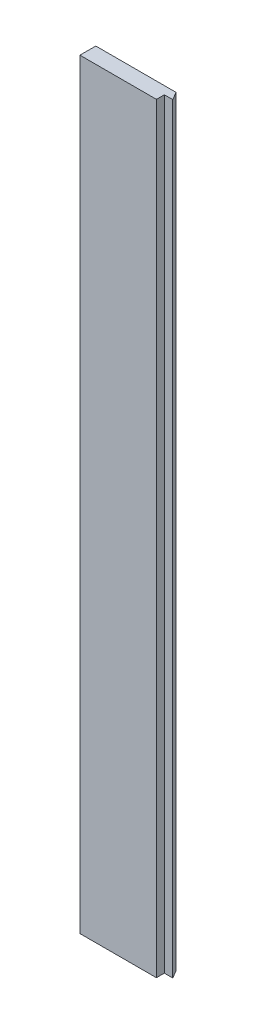
SolidWorks part; units mm, degrees
ref_plane "Front Plane" through (0, 0, 0) normal (0, 0, 1) x (1, 0, 0)
ref_plane "Top Plane" through (0, 0, 0) normal (0, 1, 0) x (1, 0, 0)
ref_plane "Right Plane" through (0, 0, 0) normal (1, 0, 0) x (0, 0, -1)
sketch "Sketch1" plane through (0, 0, 0) normal (0, 1, 0) x (1, 0, 0)
  line L0 (-60, 0) -> (-41.5, 0)
  line L1 (-60, 9) -> (60, 9)
  line L2 (-60, 9) -> (-60, -9)
  line L3 (-60, -9) -> (60, -9)
  line L4 (60, 9) -> (60, -9)
  line L5 (-60, 9) -> (60, -9) construction
  line L6 (-60, -9) -> (60, 9) construction
  line L7 (-41.5, 0) -> (-36.3038, 9)
  line L8 (-41.5, 0) -> (-41.5, 9) construction
  line L9 (60, 0) -> (54.8038, 9)
  line L10 (60, 0) -> (50.5, 0)
  line L11 (50.5, 0) -> (50.5, -9)
  line L13 (0, 9) -> (0, -9) construction
  point P0 (0, 0)
  dimension "D1" = 120
  dimension "D2" = 18
  dimension "D3" = 18.5
  dimension "D4" = 30
  dimension "D5" = 9.5
  dimension "D6" = 30
extrude "Shape" add sketch "Sketch1" along normal blind 1000
ref_plane "Plane1" [suppressed] through (-60, 790, 9) normal (0.5851, -0.811, 0) x (-0.811, -0.5851, 0)
sketch "Sketch3" [suppressed] plane through (0, 0, 9) normal (0, 0, 1) x (1, 0, 0)
  line L1 (-60, 790) -> (445, 90) construction
  line L3 (-60, 790) -> (445, 90)
  line L6 (50.5, 0) -> (60, 0)
  line L7 (60, 0) -> (60, 800)
  line L8 (60, 800) -> (50.5, 800)
  line L9 (50.5, 800) -> (50.5, 0)
  line L10 (50.5, 0) -> (60, 0)
  line L11 (60, 0) -> (60, 800)
  line L12 (60, 800) -> (50.5, 800)
  line L13 (50.5, 800) -> (50.5, 0)
  dimension "D1" = 0
extrude "Cut-Extrude1" [suppressed] cut sketch "Sketch3" against normal up to next
sketch "Sketch4" [suppressed] plane through (0, 0, 9) normal (0, 0, 1) x (1, 0, 0)
  line L0 (-170.5, 790) -> (334.5, 90) construction
  line L1 (-170.5, 790) -> (334.5, 90)
  line L6 (50.5, 0) -> (60, 0)
  line L7 (60, 0) -> (60, 800)
  line L8 (60, 800) -> (50.5, 800)
  line L9 (50.5, 800) -> (50.5, 0)
  line L10 (50.5, 0) -> (60, 0)
  line L11 (60, 0) -> (60, 800)
  line L12 (60, 800) -> (50.5, 800)
  line L13 (50.5, 800) -> (50.5, 0)
  dimension "D1" = 0
extrude "Cut-Extrude2" [suppressed] cut sketch "Sketch4" against normal through all and the other way through all
sketch "Sketch5" [suppressed] plane through (0, 0, 9) normal (0, 0, 1) x (1, 0, 0)
  line L0 (-281, 790) -> (224, 90) construction
  line L1 (-281, 790) -> (224, 90)
  line L4 (50.5, 0) -> (60, 0)
  line L5 (60, 0) -> (60, 800)
  line L6 (60, 800) -> (50.5, 800)
  line L7 (50.5, 800) -> (50.5, 0)
  line L8 (50.5, 0) -> (60, 0)
  line L9 (60, 0) -> (60, 800)
  line L10 (60, 800) -> (50.5, 800)
  line L11 (50.5, 800) -> (50.5, 0)
  dimension "D1" = 0
extrude "Cut-Extrude3" [suppressed] cut sketch "Sketch5" against normal up to next
sketch "Sketch6" [suppressed] plane through (0, 0, 9) normal (0, 0, 1) x (1, 0, 0)
  line L0 (-391.5, 790) -> (113.5, 90) construction
  line L1 (-391.5, 790) -> (113.5, 90)
  line L6 (50.5, 0) -> (60, 0)
  line L7 (60, 0) -> (60, 800)
  line L8 (60, 800) -> (50.5, 800)
  line L9 (50.5, 800) -> (50.5, 0)
  line L10 (50.5, 0) -> (60, 0)
  line L11 (60, 0) -> (60, 800)
  line L12 (60, 800) -> (50.5, 800)
  line L13 (50.5, 800) -> (50.5, 0)
  dimension "D1" = 0
extrude "Cut-Extrude4" [suppressed] cut sketch "Sketch6" against normal up to next
sketch "Sketch7" [suppressed] plane through (0, 0, 9) normal (0, 0, 1) x (1, 0, 0)
  line L0 (-502, 790) -> (3, 90) construction
  line L1 (-502, 790) -> (3, 90)
  line L2 (3, 90) -> (3, 0)
  line L3 (-60, 0) -> (50.5, 0) construction
  line L8 (50.5, 0) -> (60, 0)
  line L9 (60, 0) -> (60, 800)
  line L10 (60, 800) -> (50.5, 800)
  line L11 (50.5, 800) -> (50.5, 0)
  line L12 (50.5, 0) -> (60, 0)
  line L13 (60, 0) -> (60, 800)
  line L14 (60, 800) -> (50.5, 800)
  line L15 (50.5, 800) -> (50.5, 0)
  line M5 (-60, 0) -> (50.5, 0)
  line M6 (50.5, 0) -> (50.5, 800)
  line M7 (50.5, 800) -> (-60, 800)
  line M8 (-60, 800) -> (-60, 0)
  dimension "D1" = 0
extrude "Cut-Extrude5" [suppressed] cut sketch "Sketch7" against normal up to next contours L1 L2 M5 M6 M7 M8 | L13 L14 L12 M6
sketch "Sketch8" [suppressed] plane through (0, 0, -9) normal (0, 0, -1) x (-1, 0, 0)
  line L1 (-730.5, 863.1483) -> (129.5, 863.1483) construction
  line L8 (-730.5, 863.1483) -> (129.5, 863.1483)
  line L9 (-50.5, 0) -> (-60, 0) construction
  line L10 (-60, 0) -> (-60, 1000) construction
  line L11 (-60, 1000) -> (-50.5, 1000) construction
  line L12 (-50.5, 1000) -> (-50.5, 0) construction
  line L13 (-54.8038, 0) -> (36.3038, 0) construction
  line L14 (36.3038, 1000) -> (-54.8038, 1000) construction
  line L15 (-54.8038, 1000) -> (-54.8038, 0) construction
  line L16 (36.3038, 0) -> (41.5, 0) construction
  line L17 (41.5, 1000) -> (36.3038, 1000) construction
  line L18 (41.5, 0) -> (60, 0) construction
  line L19 (60, 0) -> (60, 1000) construction
  line L20 (60, 1000) -> (41.5, 1000) construction
  line L21 (-50.5, 0) -> (-60, 0)
  line L22 (-60, 0) -> (-60, 1000)
  line L23 (-60, 1000) -> (-50.5, 1000)
  line L24 (-50.5, 1000) -> (-50.5, 0)
  line L25 (-54.8038, 0) -> (36.3038, 0)
  line L26 (36.3038, 1000) -> (-54.8038, 1000)
  line L27 (-54.8038, 1000) -> (-54.8038, 0)
  line L28 (36.3038, 0) -> (41.5, 0)
  line L29 (41.5, 1000) -> (36.3038, 1000)
  line L30 (41.5, 0) -> (60, 0)
  line L31 (60, 0) -> (60, 1000)
  line L32 (60, 1000) -> (41.5, 1000)
extrude "Cut-Extrude6" [suppressed] cut sketch "Sketch8" against normal up to next
sketch "Sketch9" [suppressed] plane through (0, 0, -9) normal (0, 0, -1) x (-1, 0, 0)
  line L0 (-60, 1000) -> (-60, 0) construction
  line L1 (60, 1000) -> (-60, 1000)
  line L2 (60, 1000) -> (60, 863.1483)
  line L3 (60, 863.1483) -> (-60, 863.1483)
  line L4 (-60, 1000) -> (-60, 863.1483)
  line L5 (-841, 863.1483) -> (19, 863.1483) construction
  point P9 (0, 863.1483)
extrude "Cut-Extrude7" [suppressed] cut sketch "Sketch9" against normal up to next
sketch "Sketch10" plane through (0, 0, -9) normal (0, 0, -1) x (-1, 0, 0)
  line L0 (36.3038, 0) -> (-54.8038, 0) construction
  line L1 (36.3038, 1000) -> (60, 1000)
  line L2 (36.3038, 1000) -> (36.3038, 0)
  line L3 (36.3038, 0) -> (60, 0)
  line L4 (60, 1000) -> (60, 0)
  line L5 (60, 1000) -> (60, 0) construction
  line L7 (-60, 1000) -> (-60, 0) construction
  line L8 (60, 1000) -> (-60, 1000)
  line L9 (60, 1000) -> (60, 863.1483)
  line L10 (60, 863.1483) -> (-60, 863.1483)
  line L11 (-60, 1000) -> (-60, 863.1483)
  line L12 (537.107, 863.1483) -> (-71.0048, 863.1483) construction
  line M4 (36.3038, 0) -> (36.3038, 1000)
  line M5 (36.3038, 1000) -> (-54.8038, 1000)
  line M6 (-54.8038, 1000) -> (-54.8038, 0)
extrude "Cut-Extrude8" cut sketch "Sketch10" against normal up to next contours L8 L11 L10 M6 | L10 L2 M5 M6 | L10 L4 L1 L2 | L4 L10 L3 M4
